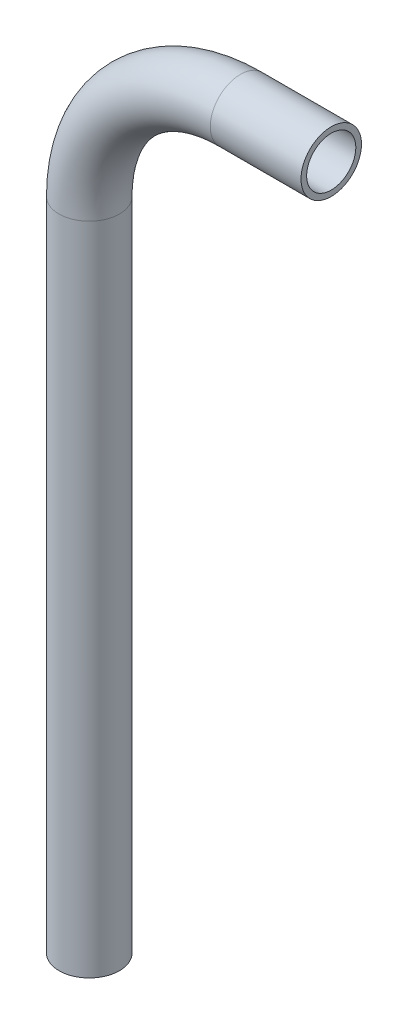
SolidWorks part; units mm, degrees
material "AISI 316 Stainless Steel Sheet (SS)"
ref_plane "Front Plane" through (0, 0, 0) normal (0, 0, 1) x (1, 0, 0)
ref_plane "Top Plane" through (0, 0, 0) normal (0, 1, 0) x (1, 0, 0)
ref_plane "Right Plane" through (0, 0, 0) normal (1, 0, 0) x (0, 0, -1)
sketch "Sketch1" plane through (0, 0, 0) normal (0, 0, 1) x (1, 0, 0)
  line L0 (0, -23.8125) -> (0, -127)
  line L1 (23.8125, 0) -> (38.1, 0)
  arc A0 (0, -23.8125) -> (23.8125, 0) centre (23.8125, -23.8125) cw
  point P6 (0, 0)
  dimension "D3" = 23.8125
  dimension "D1" = 127
  dimension "D2" = 38.1
ref_plane "Plane1" through (38.1, 0, 0) normal (1, 0, 0) x (0, 0, -1)
sketch "Sketch2" plane through (38.1, 0, 0) normal (1, 0, 0) x (0, 0, -1)
  circle A0 centre (0, 0) radius 4.7625
  circle A1 centre (0, 0) radius 3.8735
  dimension "D1" = 9.525
  dimension "D2" = 7.747
sweep "Sweep1" add profiles "Sketch2" path "Sketch1"
